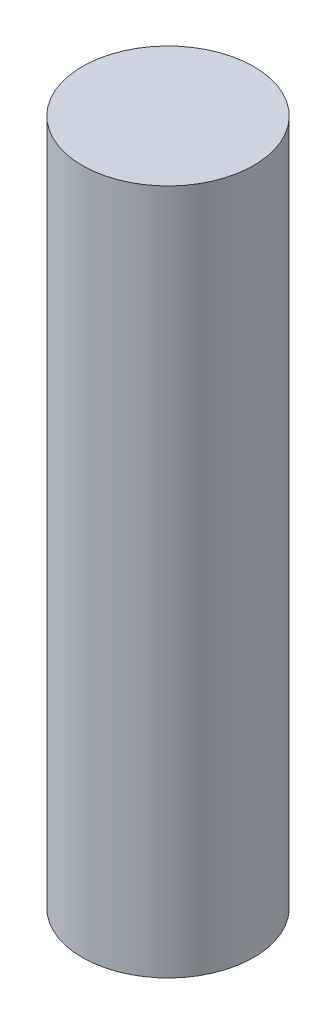
SolidWorks part; units mm, degrees
material "Acrylic (Medium-high impact)"
ref_plane "Front Plane" through (0, 0, 0) normal (0, 0, 1) x (1, 0, 0)
ref_plane "Top Plane" through (0, 0, 0) normal (0, 1, 0) x (1, 0, 0)
ref_plane "Right Plane" through (0, 0, 0) normal (1, 0, 0) x (0, 0, -1)
sketch "Sketch1" plane through (0, 0, 0) normal (0, 1, 0) x (1, 0, 0)
  circle A0 centre (0, 0) radius 1.5875
extrude "Boss-Extrude1" add sketch "Sketch1" along normal blind 12.7
